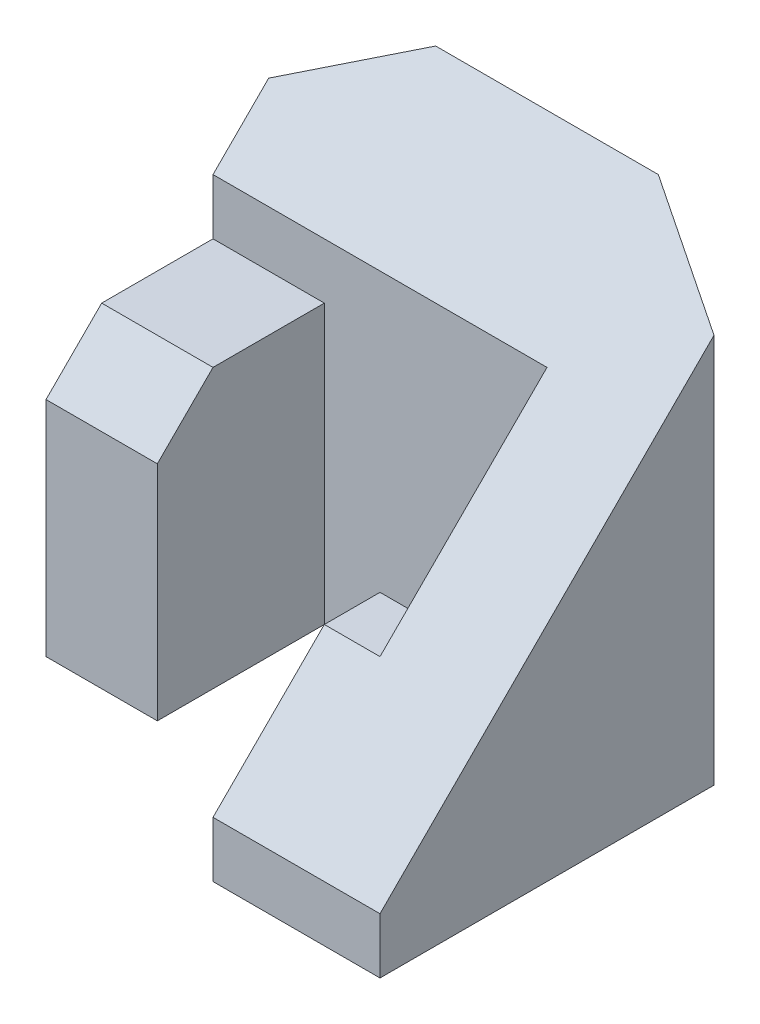
SolidWorks part; units mm, degrees
ref_plane "Front Plane" through (0, 0, 0) normal (0, 0, 1) x (1, 0, 0)
ref_plane "Top Plane" through (0, 0, 0) normal (0, 1, 0) x (1, 0, 0)
ref_plane "Right Plane" through (0, 0, 0) normal (1, 0, 0) x (0, 0, -1)
sketch "Sketch1" plane through (0, 0, 0) normal (0, 0, 1) x (1, 0, 0)
  line L1 (-20, 20) -> (20, 20)
  line L2 (-20, 20) -> (-20, -20)
  line L3 (-20, -20) -> (20, -20)
  line L4 (20, 20) -> (20, -20)
  line L5 (-20, 20) -> (20, -20) construction
  line L6 (-20, -20) -> (20, 20) construction
  point P0 (0, 0)
  dimension "D1" = 40
  dimension "D2" = 40
extrude "Boss-Extrude1" add sketch "Sketch1" along normal blind 35
sketch "Sketch2" plane through (0, 20, 0) normal (0, 1, 0) x (1, 0, 0)
  line L0 (-20, -10) -> (10, -10)
  line L1 (-20, -35) -> (-20, 0) construction
  line L2 (10, -10) -> (10, -20)
  line L3 (10, -20) -> (5, -20)
  line L4 (5, -20) -> (5, -35)
  line L5 (20, -35) -> (-20, -35) construction
  line L6 (5, -35) -> (-20, -35)
  line L7 (-20, -35) -> (-20, -10)
  line L8 (20, -35) -> (20, 0) construction
  dimension "D1" = 10
  dimension "D2" = 5
  dimension "D3" = 15
  dimension "D4" = 25
extrude "Cut-Extrude1" cut sketch "Sketch2" against normal through all
ref_plane "Plane1" through (-20, 0, 0) normal (1, 0, 0) x (0, 0, -1)
sketch "Sketch3" plane through (-20, 0, 0) normal (1, 0, 0) x (0, 0, -1)
  line L0 (0, 20) -> (-35, -15)
  line L1 (-35, -20) -> (-35, 20) construction
  line L2 (-35, -15) -> (-35, 20)
  line L3 (-35, 20) -> (0, 20)
  dimension "D1" = 5
extrude "Cut-Extrude3" cut sketch "Sketch3" along normal through all
sketch "Sketch4" plane through (5, 0, 0) normal (-1, 0, 0) x (0, 0, 1)
  line L0 (20, 0) -> (20, -5)
  line L1 (20, -20) -> (20, 0) construction
  line L2 (20, -5) -> (25, -5)
  line L3 (20, 0) -> (35, -15) construction
  line L4 (25, -5) -> (20, 0)
  dimension "D1" = 5
extrude "Cut-Extrude4" cut sketch "Sketch4" against normal blind 5
sketch "Sketch5" plane through (0, 0, 10) normal (0, 0, 1) x (1, 0, 0)
  line L0 (-20, -20) -> (-10, -20)
  line L1 (10, -20) -> (-20, -20) construction
  line L2 (-10, -20) -> (-10, 5)
  line L3 (-10, 5) -> (-20, 5)
  line L4 (-20, -20) -> (-20, 10) construction
  line L5 (-20, 5) -> (-20, -20)
  line L6 (-20, 10) -> (10, 10) construction
  dimension "D1" = 10
  dimension "D2" = 5
extrude "Boss-Extrude2" add sketch "Sketch5" along normal blind 15
sketch "Sketch6" plane through (-20, 0, 0) normal (-1, 0, 0) x (0, 0, 1)
  line L0 (25, 5) -> (20, 5)
  line L1 (25, 5) -> (10, 5) construction
  line L2 (20, 5) -> (25, 0)
  line L3 (25, 5) -> (25, -20) construction
  line L4 (25, 0) -> (25, 5)
  dimension "D1" = 5
  dimension "D2" = 5
extrude "Cut-Extrude5" cut sketch "Sketch6" against normal blind 15
sketch "Sketch7" plane through (0, -20, 0) normal (0, -1, 0) x (1, 0, 0)
  line L0 (10, 0) -> (20, 5)
  line L1 (-20, 0) -> (20, 0) construction
  line L2 (20, 35) -> (20, 0) construction
  line L3 (20, 5) -> (20, 0)
  line L4 (20, 0) -> (10, 0)
  line L5 (-20, 0) -> (-10, 0)
  line L6 (-10, 0) -> (-20, 5)
  line L7 (-20, 25) -> (-20, 0) construction
  line L8 (-20, 5) -> (-20, 0)
  dimension "D1" = 5
  dimension "D2" = 10
  dimension "D3" = 10
  dimension "D4" = 5
extrude "Cut-Extrude6" cut sketch "Sketch7" against normal through all
